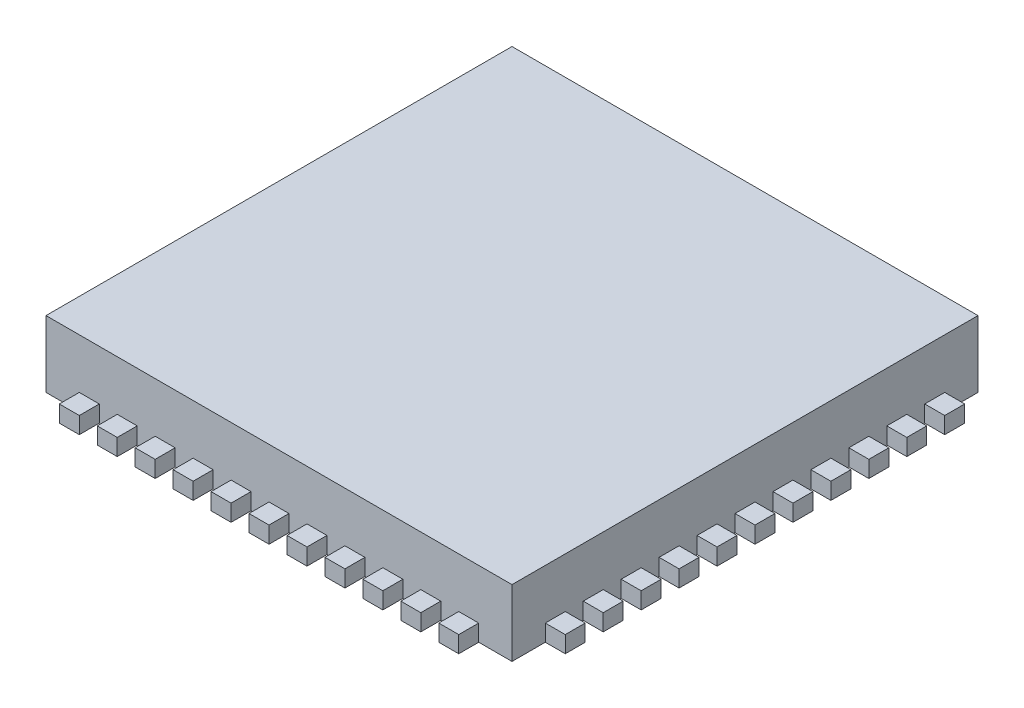
SolidWorks part; units mm, degrees
ref_plane "Front" through (0, 0, 0) normal (0, 0, 1) x (1, 0, 0)
ref_plane "Top" through (0, 0, 0) normal (0, 1, 0) x (1, 0, 0)
ref_plane "Right" through (0, 0, 0) normal (1, 0, 0) x (0, 0, -1)
sketch "Sketch1" plane through (0, 0, 0) normal (0, 1, 0) x (1, 0, 0)
  line L1 (0, 0) -> (7, 0)
  line L2 (0, 0) -> (0, 7)
  line L3 (0, 7) -> (7, 7)
  line L4 (7, 0) -> (7, 7)
  dimension "D1" = 7
extrude "Boss-Extrude1" add sketch "Sketch1" along normal blind 1
sketch "Sketch2" plane through (0, 0, 0) normal (0, 0, 1) x (1, 0, 0)
  line L0 (0, 0) -> (7, 0) construction
  line L1 (0.5, 0) -> (0.8, 0)
  line L2 (0.5, 0) -> (0.5, 0.25)
  line L3 (0.5, 0.25) -> (0.8, 0.25)
  line L4 (0.8, 0) -> (0.8, 0.25)
  line L5 (0, 1) -> (0, 0) construction
  line L6 (1.07, 0) -> (1.07, 0.25)
  line L7 (1.07, 0.25) -> (1.37, 0.25)
  line L8 (1.37, 0) -> (1.37, 0.25)
  line L9 (1.07, 0) -> (1.37, 0)
  line L10 (1.64, 0) -> (1.64, 0.25)
  line L11 (1.64, 0.25) -> (1.94, 0.25)
  line L12 (1.94, 0) -> (1.94, 0.25)
  line L13 (1.64, 0) -> (1.94, 0)
  line L14 (2.21, 0) -> (2.21, 0.25)
  line L15 (2.21, 0.25) -> (2.51, 0.25)
  line L16 (2.51, 0) -> (2.51, 0.25)
  line L17 (2.21, 0) -> (2.51, 0)
  line L18 (2.78, 0) -> (2.78, 0.25)
  line L19 (2.78, 0.25) -> (3.08, 0.25)
  line L20 (3.08, 0) -> (3.08, 0.25)
  line L21 (2.78, 0) -> (3.08, 0)
  line L22 (3.35, 0) -> (3.35, 0.25)
  line L23 (3.35, 0.25) -> (3.65, 0.25)
  line L24 (3.65, 0) -> (3.65, 0.25)
  line L25 (3.35, 0) -> (3.65, 0)
  line L26 (3.92, 0) -> (3.92, 0.25)
  line L27 (3.92, 0.25) -> (4.22, 0.25)
  line L28 (4.22, 0) -> (4.22, 0.25)
  line L29 (3.92, 0) -> (4.22, 0)
  line L30 (4.49, 0) -> (4.49, 0.25)
  line L31 (4.49, 0.25) -> (4.79, 0.25)
  line L32 (4.79, 0) -> (4.79, 0.25)
  line L33 (4.49, 0) -> (4.79, 0)
  line L34 (5.06, 0) -> (5.06, 0.25)
  line L35 (5.06, 0.25) -> (5.36, 0.25)
  line L36 (5.36, 0) -> (5.36, 0.25)
  line L37 (5.06, 0) -> (5.36, 0)
  line L38 (5.63, 0) -> (5.63, 0.25)
  line L39 (5.63, 0.25) -> (5.93, 0.25)
  line L40 (5.93, 0) -> (5.93, 0.25)
  line L41 (5.63, 0) -> (5.93, 0)
  line L42 (6.2, 0) -> (6.2, 0.25)
  line L43 (6.2, 0.25) -> (6.5, 0.25)
  line L44 (6.5, 0) -> (6.5, 0.25)
  line L45 (6.2, 0) -> (6.5, 0)
  line L46 (7, 1) -> (7, 0) construction
  dimension "D1" = 0.5
  dimension "D3" = 0.5
  dimension "D4" = 0.3
  dimension "D5" = 0.25
  dimension "D2" = 11
extrude "Boss-Extrude2" add sketch "Sketch2" along normal blind 0.3
sketch "Sketch3" plane through (7, 0, 0) normal (1, 0, 0) x (0, 0, -1)
  line L1 (0, 0) -> (7, 0) construction
  line L2 (0.5, 0) -> (0.8, 0)
  line L3 (0.5, 0) -> (0.5, 0.25)
  line L4 (0.5, 0.25) -> (0.8, 0.25)
  line L7 (0.8, 0) -> (0.8, 0.25)
  line L8 (0, 1) -> (0, 0) construction
  line L9 (1.07, 0.25) -> (1.37, 0.25)
  line L10 (1.07, 0) -> (1.07, 0.25)
  line L11 (1.07, 0) -> (1.37, 0)
  line L12 (1.37, 0) -> (1.37, 0.25)
  line L13 (1.64, 0.25) -> (1.94, 0.25)
  line L14 (1.64, 0) -> (1.64, 0.25)
  line L15 (1.64, 0) -> (1.94, 0)
  line L16 (1.94, 0) -> (1.94, 0.25)
  line L17 (2.21, 0.25) -> (2.51, 0.25)
  line L18 (2.21, 0) -> (2.21, 0.25)
  line L19 (2.21, 0) -> (2.51, 0)
  line L20 (2.51, 0) -> (2.51, 0.25)
  line L21 (2.78, 0.25) -> (3.08, 0.25)
  line L22 (2.78, 0) -> (2.78, 0.25)
  line L23 (2.78, 0) -> (3.08, 0)
  line L24 (3.08, 0) -> (3.08, 0.25)
  line L25 (3.35, 0.25) -> (3.65, 0.25)
  line L26 (3.35, 0) -> (3.35, 0.25)
  line L27 (3.35, 0) -> (3.65, 0)
  line L28 (3.65, 0) -> (3.65, 0.25)
  line L29 (3.92, 0.25) -> (4.22, 0.25)
  line L30 (3.92, 0) -> (3.92, 0.25)
  line L31 (3.92, 0) -> (4.22, 0)
  line L32 (4.22, 0) -> (4.22, 0.25)
  line L33 (4.49, 0.25) -> (4.79, 0.25)
  line L34 (4.49, 0) -> (4.49, 0.25)
  line L35 (4.49, 0) -> (4.79, 0)
  line L36 (4.79, 0) -> (4.79, 0.25)
  line L37 (5.06, 0.25) -> (5.36, 0.25)
  line L38 (5.06, 0) -> (5.06, 0.25)
  line L39 (5.06, 0) -> (5.36, 0)
  line L40 (5.36, 0) -> (5.36, 0.25)
  line L41 (5.63, 0.25) -> (5.93, 0.25)
  line L42 (5.63, 0) -> (5.63, 0.25)
  line L43 (5.63, 0) -> (5.93, 0)
  line L44 (5.93, 0) -> (5.93, 0.25)
  line L45 (6.2, 0.25) -> (6.5, 0.25)
  line L46 (6.2, 0) -> (6.2, 0.25)
  line L52 (6.2, 0) -> (6.5, 0)
  line L53 (6.5, 0) -> (6.5, 0.25)
  line L54 (7, 1) -> (7, 0) construction
  dimension "D1" = 0.5
  dimension "D2" = 11
  dimension "D3" = 0.5
  dimension "D5" = 0.25
  dimension "D4" = 0.3
extrude "Boss-Extrude3" add sketch "Sketch3" along normal blind 0.3
sketch "Sketch4" plane through (0, 0, -7) normal (0, 0, -1) x (-1, 0, 0)
  line L0 (-7, 0) -> (0, 0) construction
  line L1 (-6.5, 0) -> (-6.2, 0)
  line L2 (-6.5, 0) -> (-6.5, 0.25)
  line L3 (-6.5, 0.25) -> (-6.2, 0.25)
  line L4 (-6.2, 0) -> (-6.2, 0.25)
  line L5 (-7, 1) -> (-7, 0) construction
  line L6 (-5.93, 0.25) -> (-5.63, 0.25)
  line L7 (-5.93, 0) -> (-5.93, 0.25)
  line L8 (-5.63, 0) -> (-5.63, 0.25)
  line L9 (-5.93, 0) -> (-5.63, 0)
  line L10 (-5.36, 0.25) -> (-5.06, 0.25)
  line L11 (-5.36, 0) -> (-5.36, 0.25)
  line L12 (-5.06, 0) -> (-5.06, 0.25)
  line L13 (-5.36, 0) -> (-5.06, 0)
  line L14 (-4.79, 0.25) -> (-4.49, 0.25)
  line L15 (-4.79, 0) -> (-4.79, 0.25)
  line L16 (-4.49, 0) -> (-4.49, 0.25)
  line L17 (-4.79, 0) -> (-4.49, 0)
  line L18 (-4.22, 0.25) -> (-3.92, 0.25)
  line L19 (-4.22, 0) -> (-4.22, 0.25)
  line L20 (-3.92, 0) -> (-3.92, 0.25)
  line L21 (-4.22, 0) -> (-3.92, 0)
  line L22 (-3.65, 0.25) -> (-3.35, 0.25)
  line L23 (-3.65, 0) -> (-3.65, 0.25)
  line L24 (-3.35, 0) -> (-3.35, 0.25)
  line L25 (-3.65, 0) -> (-3.35, 0)
  line L26 (-3.08, 0.25) -> (-2.78, 0.25)
  line L27 (-3.08, 0) -> (-3.08, 0.25)
  line L28 (-2.78, 0) -> (-2.78, 0.25)
  line L29 (-3.08, 0) -> (-2.78, 0)
  line L30 (-2.51, 0.25) -> (-2.21, 0.25)
  line L31 (-2.51, 0) -> (-2.51, 0.25)
  line L32 (-2.21, 0) -> (-2.21, 0.25)
  line L33 (-2.51, 0) -> (-2.21, 0)
  line L34 (-1.94, 0.25) -> (-1.64, 0.25)
  line L35 (-1.94, 0) -> (-1.94, 0.25)
  line L36 (-1.64, 0) -> (-1.64, 0.25)
  line L37 (-1.94, 0) -> (-1.64, 0)
  line L38 (-1.37, 0.25) -> (-1.07, 0.25)
  line L39 (-1.37, 0) -> (-1.37, 0.25)
  line L40 (-1.07, 0) -> (-1.07, 0.25)
  line L41 (-1.37, 0) -> (-1.07, 0)
  line L42 (-0.8, 0.25) -> (-0.5, 0.25)
  line L43 (-0.8, 0) -> (-0.8, 0.25)
  line L44 (-0.5, 0) -> (-0.5, 0.25)
  line L45 (-0.8, 0) -> (-0.5, 0)
  line L46 (0, 1) -> (0, 0) construction
  dimension "D1" = 0.5
  dimension "D2" = 0.25
  dimension "D3" = 0.3
  dimension "D4" = 11
  dimension "D5" = 0.5
extrude "Boss-Extrude4" add sketch "Sketch4" along normal blind 0.3
sketch "Sketch5" plane through (0, 0, 0) normal (-1, 0, 0) x (0, 0, 1)
  line L0 (-7, 0) -> (0, 0) construction
  line L1 (-6.5, 0) -> (-6.2, 0)
  line L2 (-6.5, 0) -> (-6.5, 0.25)
  line L3 (-6.5, 0.25) -> (-6.2, 0.25)
  line L4 (-6.2, 0) -> (-6.2, 0.25)
  line L5 (-7, 1) -> (-7, 0) construction
  line L6 (-5.93, 0.25) -> (-5.63, 0.25)
  line L7 (-5.93, 0) -> (-5.93, 0.25)
  line L8 (-5.63, 0) -> (-5.63, 0.25)
  line L9 (-5.93, 0) -> (-5.63, 0)
  line L10 (-5.36, 0.25) -> (-5.06, 0.25)
  line L11 (-5.36, 0) -> (-5.36, 0.25)
  line L12 (-5.06, 0) -> (-5.06, 0.25)
  line L13 (-5.36, 0) -> (-5.06, 0)
  line L14 (-4.79, 0.25) -> (-4.49, 0.25)
  line L15 (-4.79, 0) -> (-4.79, 0.25)
  line L16 (-4.49, 0) -> (-4.49, 0.25)
  line L17 (-4.79, 0) -> (-4.49, 0)
  line L18 (-4.22, 0.25) -> (-3.92, 0.25)
  line L19 (-4.22, 0) -> (-4.22, 0.25)
  line L20 (-3.92, 0) -> (-3.92, 0.25)
  line L21 (-4.22, 0) -> (-3.92, 0)
  line L22 (-3.65, 0.25) -> (-3.35, 0.25)
  line L23 (-3.65, 0) -> (-3.65, 0.25)
  line L24 (-3.35, 0) -> (-3.35, 0.25)
  line L25 (-3.65, 0) -> (-3.35, 0)
  line L26 (-3.08, 0.25) -> (-2.78, 0.25)
  line L27 (-3.08, 0) -> (-3.08, 0.25)
  line L28 (-2.78, 0) -> (-2.78, 0.25)
  line L29 (-3.08, 0) -> (-2.78, 0)
  line L30 (-2.51, 0.25) -> (-2.21, 0.25)
  line L31 (-2.51, 0) -> (-2.51, 0.25)
  line L32 (-2.21, 0) -> (-2.21, 0.25)
  line L33 (-2.51, 0) -> (-2.21, 0)
  line L34 (-1.94, 0.25) -> (-1.64, 0.25)
  line L35 (-1.94, 0) -> (-1.94, 0.25)
  line L36 (-1.64, 0) -> (-1.64, 0.25)
  line L37 (-1.94, 0) -> (-1.64, 0)
  line L38 (-1.37, 0.25) -> (-1.07, 0.25)
  line L39 (-1.37, 0) -> (-1.37, 0.25)
  line L40 (-1.07, 0) -> (-1.07, 0.25)
  line L41 (-1.37, 0) -> (-1.07, 0)
  line L42 (-0.8, 0.25) -> (-0.5, 0.25)
  line L43 (-0.8, 0) -> (-0.8, 0.25)
  line L44 (-0.5, 0) -> (-0.5, 0.25)
  line L45 (-0.8, 0) -> (-0.5, 0)
  line L46 (0, 1) -> (0, 0) construction
  dimension "D1" = 0.5
  dimension "D2" = 0.3
  dimension "D3" = 0.25
  dimension "D5" = 0.5
  dimension "D4" = 11
extrude "Boss-Extrude5" add sketch "Sketch5" along normal blind 0.3
